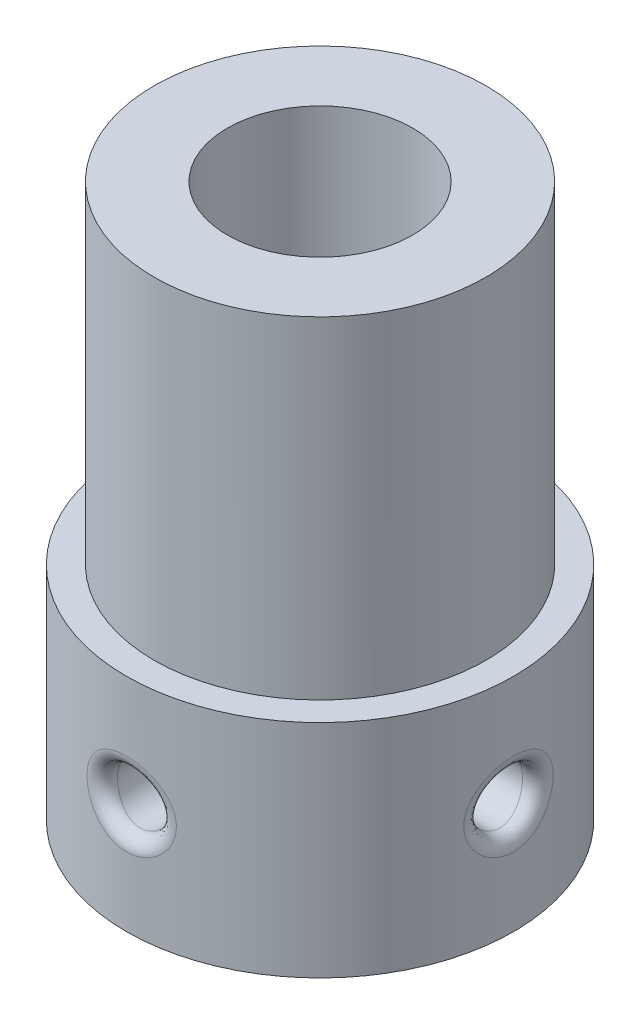
SolidWorks part; units mm, degrees
ref_plane "Front Plane" through (0, 0, 0) normal (0, 0, 1) x (1, 0, 0)
ref_plane "Top Plane" through (0, 0, 0) normal (0, 1, 0) x (1, 0, 0)
ref_plane "Right Plane" through (0, 0, 0) normal (1, 0, 0) x (0, 0, -1)
sketch "Sketch1" plane through (0, 0, 0) normal (0, 1, 0) x (1, 0, 0)
  line L0 (0, 0) -> (-13523.7469, 0) construction
  line L1 (0, 0) -> (0, 13523.7469) construction
  line L2 (7, 0) -> (44203.7332, -23380.5212) construction
  circle A0 centre (0, 0) radius 7
  dimension "D1" = 14
extrude "Boss-Extrude1" add sketch "Sketch1" along normal blind 8
sketch "Sketch2" plane through (0, 8, 0) normal (0, 1, 0) x (1, 0, 0)
  circle A0 centre (0, 0) radius 6
  dimension "D1" = 12
extrude "Boss-Extrude2" add sketch "Sketch2" along normal blind 14
sketch "Sketch3" plane through (0, 22, 0) normal (0, 1, 0) x (1, 0, 0)
  circle A0 centre (0, 0) radius 7
  dimension "D1" = 14
sketch "Sketch6" plane through (0, 0, 0) normal (0, -1, 0) x (1, 0, 0)
  circle A0 centre (0, 0) radius 3
  dimension "D1" = 6
extrude "Cut-Extrude2" cut sketch "Sketch6" against normal blind 20
sketch "Sketch7" plane through (0, 0, 0) normal (0, -1, 0) x (1, 0, 0)
  line L0 (0, 3) -> (0, 7) construction
  circle A0 centre (0, 0) radius 3 construction
  circle A1 centre (0, 0) radius 7 construction
ref_plane "Plane1" through (0, 0, 7) normal (0, 0, 1) x (1, 0, 0)
sketch "Sketch8" plane through (0, 0, 7) normal (0, 0, 1) x (1, 0, 0)
  line L0 (0, 0) -> (0, 50000) construction
  circle A0 centre (0, 4) radius 1
  dimension "D1" = 2
extrude "Cut-Extrude3" cut sketch "Sketch8" against normal up to next
pattern_circular "CirPattern1" count 2 every 90 about axis through (0, 0, 0) along (0, 1, 0) of "Cut-Extrude3"
fillet "Fillet1" radius 0.5 2 edges at (6.9317, 3.7814, 0.9758) (-0.9758, 3.7814, 6.9317)
extrude "ｶｯﾄ - 押し出し2" cut sketch "Sketch3" against normal up to surface (2 mm away) contours A0 up to face at (0, 20, -3)
scale "ｽｹｰﾙ1" scale about centroid uniform scaling yes scale factor 0.894737
sketch "ｽｹｯﾁ1" plane through (0, 0.9576, 0) normal (0, -1, 0) x (1, 0, 0)
  circle A0 centre (0, 0) radius 3
  dimension "D1" = 6
extrude "ｶｯﾄ - 押し出し3" cut sketch "ｽｹｯﾁ1" against normal through all
